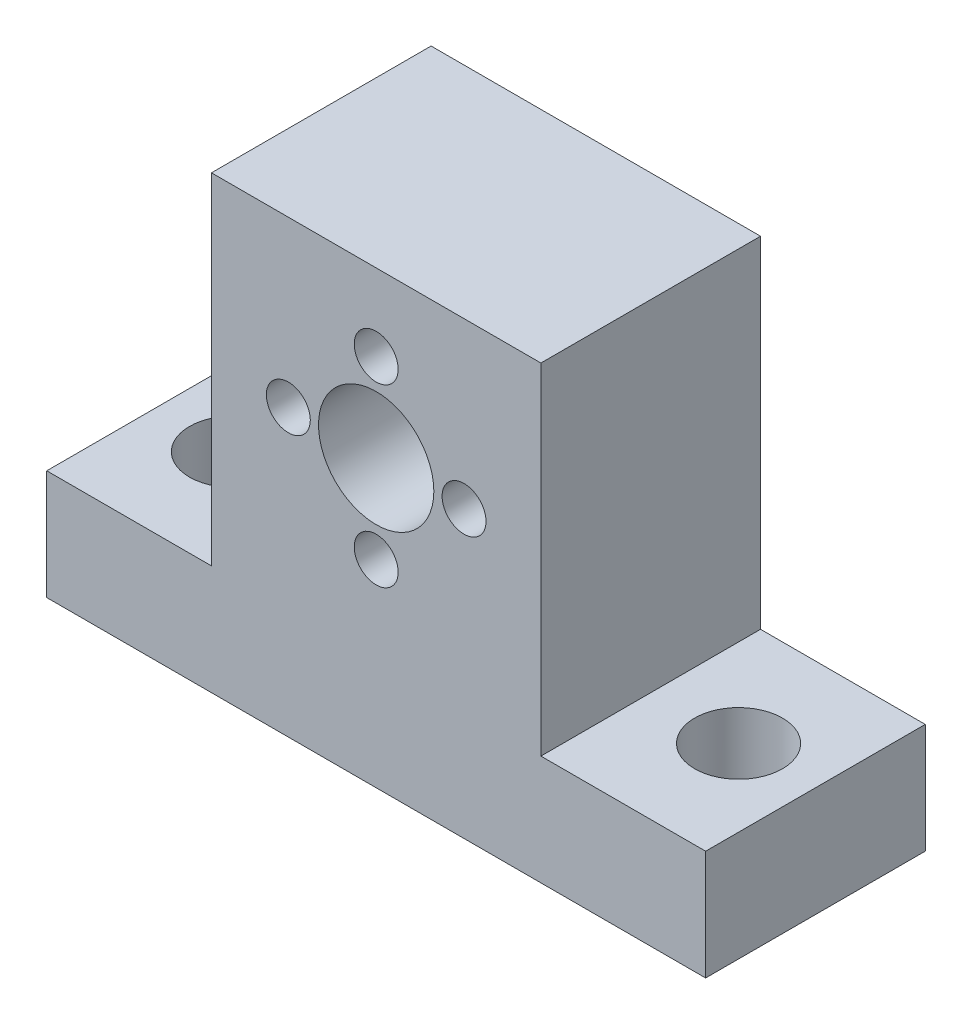
SolidWorks part; units mm, degrees
ref_plane "Front Plane" through (0, 0, 0) normal (0, 0, 1) x (1, 0, 0)
ref_plane "Top Plane" through (0, 0, 0) normal (0, 1, 0) x (1, 0, 0)
ref_plane "Right Plane" through (0, 0, 0) normal (1, 0, 0) x (0, 0, -1)
sketch "Sketch1" plane through (0, 0, 0) normal (0, 0, 1) x (1, 0, 0)
  line L0 (0, -438.3722) -> (0, 21480.2356) construction
  line L1 (-438.3722, 0) -> (21480.2356, 0) construction
  line L3 (-30, -26) -> (30, -26)
  line L4 (-30, -26) -> (-30, 15)
  line L5 (-30, 15) -> (30, 15)
  line L6 (30, -26) -> (30, 15)
  circle A0 centre (0, 0) radius 5.25
  circle A1 centre (0, 0) radius 8 construction
  circle A2 centre (0, 8) radius 2
  circle A3 centre (8, 0) radius 2
  circle A4 centre (0, -8) radius 2
  circle A5 centre (-8, 0) radius 2
  point P4 (0, 0)
  point P24 (0, 0)
  dimension "D2" = 10.5
  dimension "D4" = 16
  dimension "D5" = 4
  dimension "D7" = 8
  dimension "D8" = 8
  dimension "D1" = 15
  dimension "D3" = 60
  dimension "D9" = 26
  dimension "D10" = 30
  dimension "D6" = 4
extrude "Boss-Extrude1" add sketch "Sketch1" along normal blind 20
sketch "Sketch2" plane through (0, 15, 0) normal (0, 1, 0) x (1, 0, 0)
  line L0 (0, -1000) -> (0, 49000) construction
  line L1 (-1030, -10) -> (48970, -10) construction
  line L2 (-30, -20) -> (-30, 0) construction
  circle A0 centre (-23, -10) radius 4
  circle A1 centre (23, -10) radius 4
  point P8 (-30, -10)
  dimension "D2" = 8
  dimension "D1" = 7
extrude "Cut-Extrude1" cut sketch "Sketch2" against normal through all
sketch "Sketch3" plane through (0, 0, 0) normal (0, 0, -1) x (-1, 0, 0)
  line L0 (0, -1000) -> (0, 49000) construction
  line L1 (-1000, 0) -> (49000, 0) construction
  line L2 (-30, 15) -> (30, 15) construction
  line L3 (30, -26) -> (15, -26)
  line L4 (30, -26) -> (30, 15)
  line L5 (30, 15) -> (15, 15)
  line L6 (15, -26) -> (15, 15)
  line L7 (30, -16) -> (15, -16)
  line L8 (-30, -16) -> (-15, -16)
  line L9 (-15, -26) -> (-15, 15)
  line L10 (-30, 15) -> (-15, 15)
  line L11 (-30, -26) -> (-30, 15)
  line L12 (-30, -26) -> (-15, -26)
  line M7 (-30, 15) -> (-30, -26)
  line M10 (30, 15) -> (-30, 15)
  dimension "D1" = 15
  dimension "D2" = 10
extrude "Cut-Extrude2" cut sketch "Sketch3" against normal through all contours L7 L4 L6 M10 | L8 L9 M10 M7
